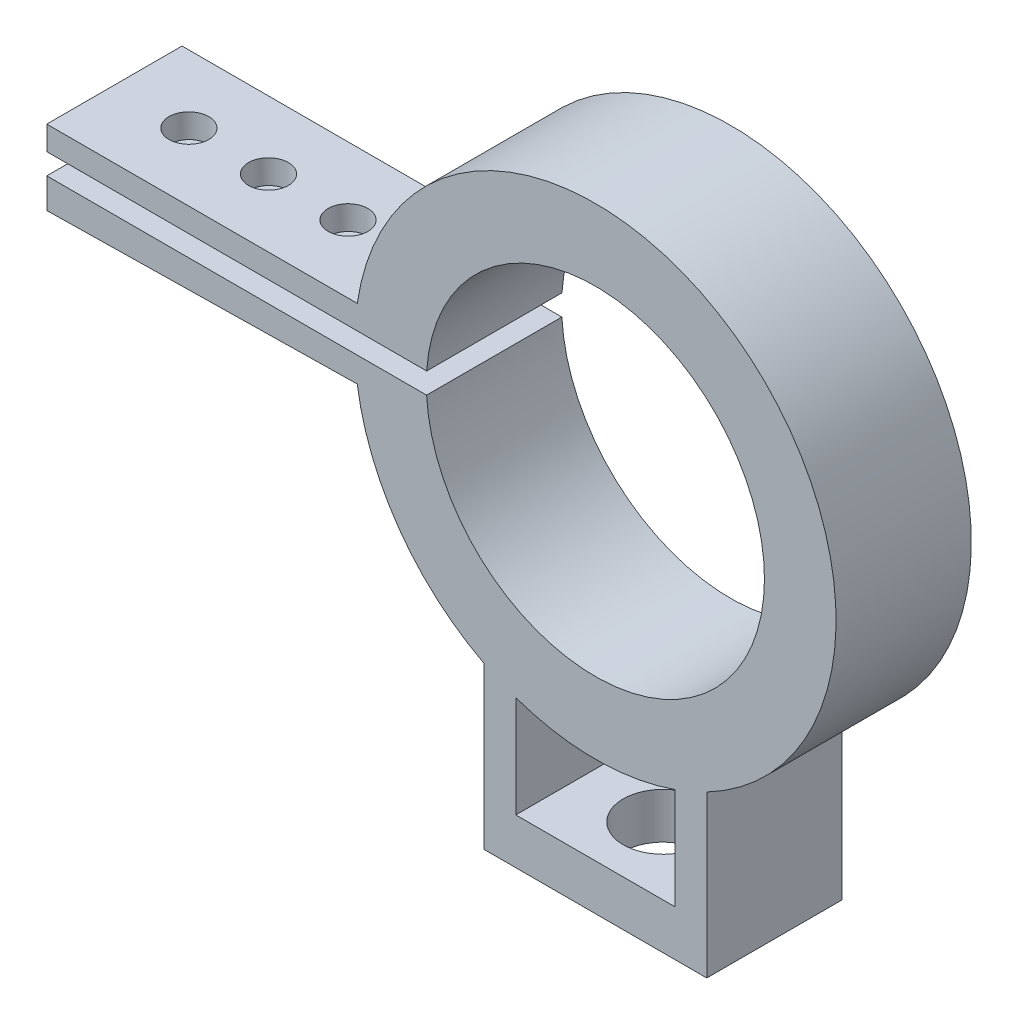
SolidWorks part; units mm, degrees
ref_plane "Front Plane" through (0, 0, 0) normal (0, 0, 1) x (1, 0, 0)
ref_plane "Top Plane" through (0, 0, 0) normal (0, 1, 0) x (1, 0, 0)
ref_plane "Right Plane" through (0, 0, 0) normal (1, 0, 0) x (0, 0, -1)
sketch "Sketch1" plane through (0, 0, 0) normal (0, 0, 1) x (1, 0, 0)
  line L0 (0, 0) -> (-30.25, 0) construction
  line L1 (0, 0) -> (0, 4.4054)
  line L2 (0, 0) -> (0, -5)
  line L3 (-68.9508, -5) -> (-20.8254, -4.2267)
  line L4 (-68.9508, -5) -> (-68.9508, 4.4054)
  line L5 (-68.9508, 4.4054) -> (-20.7883, 4.4054)
  line L6 (-20.7883, 4.4054) -> (-20.7883, 1.4054)
  line L7 (-20.7883, 1.4054) -> (-68.9508, 1.4054)
  line L8 (-20.8254, -4.2267) -> (-20.8254, -1.2267)
  line L9 (-20.8254, -1.2267) -> (-68.9508, -1.2267)
  line L10 (0, 0) -> (0, -21.25)
  line L11 (0, -21.25) -> (14, -21.25)
  line L12 (0, -21.25) -> (-14, -21.25)
  line L13 (-14, -21.25) -> (-14, -47.0603)
  line L14 (-14, -47.0603) -> (14, -47.0603)
  line L15 (14, -47.0603) -> (14, -21.25)
  line L16 (-10, -47.0603) -> (-10, -21.25)
  line L17 (10, -21.25) -> (10, -47.0603)
  line L18 (10, -41.3103) -> (-10, -41.3103)
  circle A0 centre (0, 0) radius 21.25
  circle A1 centre (0, 0) radius 30.25
  dimension "D1" = 9
  dimension "D2" = 42.5
  dimension "D3" = 4
  dimension "D4" = 4
  dimension "D5" = 14
  dimension "D6" = 14
  dimension "D7" = 5.75
extrude "Boss-Extrude1" add sketch "Sketch1" along normal blind 17 contours L9 A1 L3 A0 | A1 L9 L4 L3 | A1 L5 L4 L7 | L5 A1 L7 A0 | L15 A1 L5 A0 L11 | L3 A1 L13 L12 A0 | L13 A1 L16 L12 | L16 A1 L17 L11 L12 | L17 A1 L15 L11 | A1 L17 L14 L15 | A1 L13 L14 L16 | L17 L18 L16 L14
sketch "Sketch2" plane through (0, -47.0603, 0) normal (0, -1, 0) x (1, 0, 0)
  line L0 (0, 17) -> (0, 0) construction
  line L1 (-14, 17) -> (14, 17) construction
  line L2 (-14, 0) -> (14, 0) construction
  circle A0 centre (0, 8.5) radius 5
extrude "Cut-Extrude2" cut sketch "Sketch2" against normal blind 7
sketch "Sketch4" plane through (0.0625, -3.8911, 0) normal (0.0161, -0.9999, 0) x (0.9999, 0.0161, 0)
  line L0 (-49.5104, 17) -> (-49.5104, 0) construction
  line L1 (-69.0222, 17) -> (-29.9986, 17) construction
  line L2 (-69.0222, 0) -> (-29.9986, 0) construction
  circle A0 centre (-49.5104, 8.5) radius 2.5
  circle A1 centre (-39.5104, 8.5) radius 2.5
  circle A2 centre (-59.5104, 8.5) radius 2.5
  dimension "D1" = 2
  dimension "D2" = 2
extrude "Cut-Extrude3" cut sketch "Sketch4" against normal blind 17
